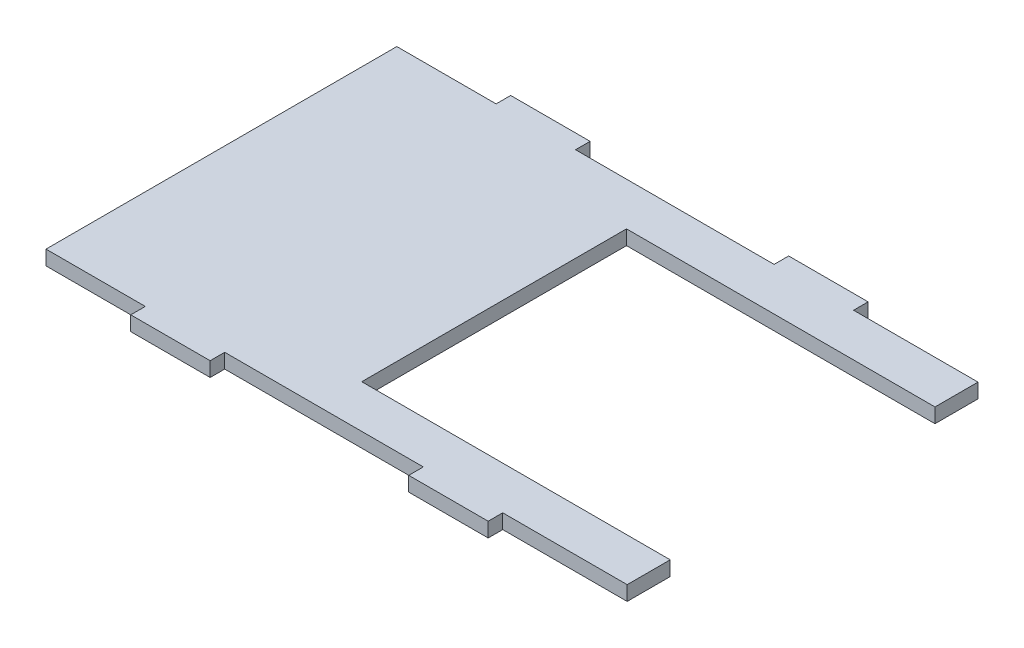
SolidWorks part; units mm, degrees
ref_plane "Front Plane" through (0, 0, 0) normal (0, 0, 1) x (1, 0, 0)
ref_plane "Top Plane" through (0, 0, 0) normal (0, 1, 0) x (1, 0, 0)
ref_plane "Right Plane" through (0, 0, 0) normal (1, 0, 0) x (0, 0, -1)
sketch "Sketch2" plane through (0, 0, 0) normal (0, 1, 0) x (1, 0, 0)
  line L0 (111.506, 59.055) -> (111.506, 67.31)
  line L1 (0, 0) -> (19.05, 0)
  line L2 (0, 0) -> (0, 67.31)
  line L3 (0, 67.31) -> (19.05, 67.31)
  line L4 (111.506, 0) -> (111.506, 8.255)
  line L5 (111.506, 8.255) -> (52.324, 8.255)
  line L6 (34.29, 67.31) -> (72.39, 67.31)
  line L7 (111.506, 59.055) -> (52.324, 59.055)
  line L8 (52.324, 8.255) -> (52.324, 59.055)
  line L9 (19.05, 70.104) -> (34.29, 70.104)
  line L10 (19.05, 70.104) -> (19.05, 67.31)
  line L11 (87.63, 67.31) -> (111.506, 67.31)
  line L12 (34.29, 70.104) -> (34.29, 67.31)
  line L13 (72.39, 70.104) -> (87.63, 70.104)
  line L14 (72.39, 70.104) -> (72.39, 67.31)
  line L15 (87.63, 0) -> (111.506, 0)
  line L16 (87.63, 70.104) -> (87.63, 67.31)
  line L18 (19.05, 0) -> (19.05, -2.794)
  line L19 (19.05, -2.794) -> (34.29, -2.794)
  line L20 (34.29, 0) -> (34.29, -2.794)
  line L21 (34.29, 0) -> (72.39, 0)
  line L22 (72.39, 0) -> (72.39, -2.794)
  line L23 (72.39, -2.794) -> (87.63, -2.794)
  line L24 (87.63, 0) -> (87.63, -2.794)
  point P4 (111.506, 33.655)
  dimension "D1" = 111.506
  dimension "D2" = 67.31
  dimension "D3" = 59.182
  dimension "D4" = 50.8
  dimension "D5" = 15.24
  dimension "D6" = 19.05
  dimension "D7" = 2.794
  dimension "D8" = 38.1
  dimension "D9" = 15.24
  dimension "D10" = 15.24
extrude "Boss-Extrude1" add sketch "Sketch2" along normal blind 2.794
